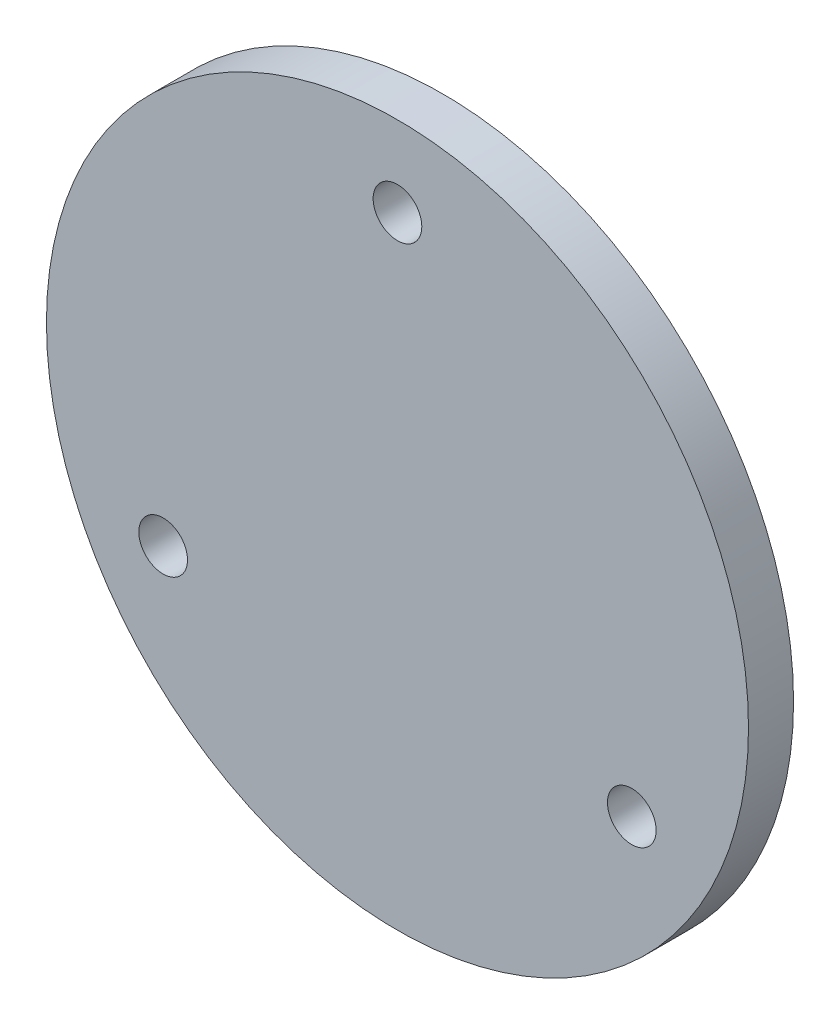
SolidWorks part; units mm, degrees
ref_plane "Front Plane" through (0, 0, 0) normal (0, 0, 1) x (1, 0, 0)
ref_plane "Top Plane" through (0, 0, 0) normal (0, 1, 0) x (1, 0, 0)
ref_plane "Right Plane" through (0, 0, 0) normal (1, 0, 0) x (0, 0, -1)
sketch "Sketch1" plane through (0, 0, 0) normal (0, 0, 1) x (1, 0, 0)
  circle A0 centre (0, 0) radius 49.4665
  dimension "D1" = 98.933
extrude "Boss-Extrude1" add sketch "Sketch1" along normal blind 6.35
sketch "Sketch2" [suppressed] plane through (0, 0, 6.35) normal (0, 0, 1) x (1, 0, 0)
  line L0 (-15.5, -30.74) -> (15.5, 0.26) construction
  line L1 (-15.5, 0.26) -> (15.5, 0.26)
  line L2 (-15.5, 0.26) -> (-15.5, -30.74)
  line L3 (-15.5, -30.74) -> (15.5, -30.74)
  line L4 (15.5, 0.26) -> (15.5, -30.74)
  point P4 (0, -15.24)
  point P5 (0, 0.26)
  dimension "D1" = 31
  dimension "D2" = 31
  dimension "D3" = 15.24
hole_wizard "Ø3.0mm Dowel Hole1" [suppressed] positions "Sketch3" profile "Sketch4" hole size "Ø3.0" standard "ANSI Metric"
sketch "Sketch3" [suppressed] plane through (0, 0, 6.35) normal (0, 0, 1) x (1, 0, 0)
  point P0 (15.5, 0.26)
  point P3 (-15.5, 0.26)
  point P6 (-15.5, -30.74)
  point P9 (15.5, -30.74)
sketch "Sketch4" plane through (15.5, 0.26, 6.35) normal (1, 0, 0) x (0, -1, 0)
  line L0 (0, 0) -> (0, 6.35)
  line L1 (0, 6.35) -> (1.5, 6.35)
  line L2 (1.5, 6.35) -> (1.5, 0)
  line L5 (1.5, 0) -> (0, 0)
  line L11 (0, -6.35) -> (0, 107.95) construction
  dimension "Thru Hole Dia." = 3
  dimension "Thru Hole Depth" = 6.35
sketch "Sketch5" [suppressed] plane through (0, 0, 6.35) normal (0, 0, 1) x (1, 0, 0)
  line L0 (-15.5, -30.74) -> (15.5, 0.26) construction
  line L1 (-21.15, 5.91) -> (21.15, 5.91)
  line L2 (-21.15, 5.91) -> (-21.15, -36.39)
  line L3 (-21.15, -36.39) -> (21.15, -36.39)
  line L4 (21.15, 5.91) -> (21.15, -36.39)
  line L5 (-21.15, 5.91) -> (21.15, -36.39) construction
  line L6 (-21.15, -36.39) -> (21.15, 5.91) construction
  circle A0 centre (0, -42.74) radius 3.175
  circle A1 centre (0, 12.26) radius 3.175
  point P0 (0, -15.24)
  point P7 (0, -15.24)
  dimension "D3" = 6.35
  dimension "D5" = 6.35
  dimension "D1" = 42.3
  dimension "D2" = 42.3
  dimension "D4" = 6.35
  dimension "D6" = 6.35
extrude "Cut-Extrude1" [suppressed] cut sketch "Sketch5" against normal through all contours A0 | A1
sketch "Sketch6" plane through (0, 0, 6.35) normal (0, 0, 1) x (1, 0, 0)
  line L0 (0, 38.1282) -> (-33.02, -19.0641) construction
  line L1 (-33.02, -19.0641) -> (33.02, -19.0641) construction
  line L2 (33.02, -19.0641) -> (0, 38.1282) construction
  line L3 (-33.02, -19.0641) -> (0, 0) construction
  line L4 (0, 0) -> (33.02, -19.0641) construction
  line L5 (0, 0) -> (0, 38.1282) construction
  circle A0 centre (0, 38.1282) radius 3.429
  circle A1 centre (-33.02, -19.0641) radius 3.429
  circle A2 centre (33.02, -19.0641) radius 3.429
  dimension "D1" = 6.858
  dimension "D2" = 66.04
  dimension "D3" = 60
  dimension "D4" = 60
extrude "Cut-Extrude2" cut sketch "Sketch6" against normal through all
sketch "Sketch8" [suppressed] plane through (0, 0, 6.35) normal (0, 0, 1) x (1, 0, 0)
  line L0 (-15.5, -30.74) -> (15.5, 0.26) construction
  circle A0 centre (0, -15.24) radius 11.049
  point P4 (0, -15.24)
  dimension "D1" = 22.098
extrude "Cut-Extrude3" [suppressed] cut sketch "Sketch8" against normal through all
